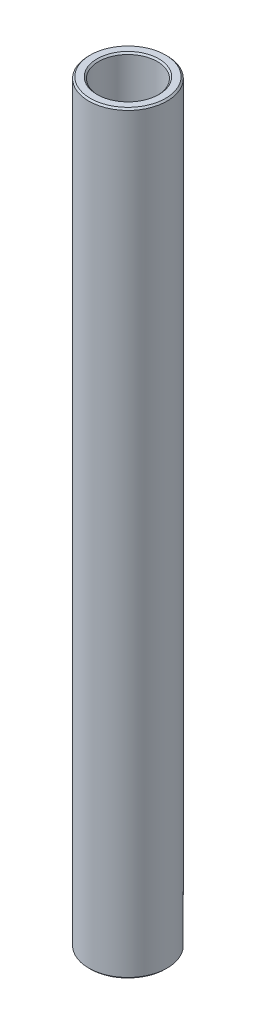
SolidWorks part; units mm, degrees
ref_plane "Front Plane" through (0, 0, 0) normal (0, 0, 1) x (1, 0, 0)
ref_plane "Top Plane" through (0, 0, 0) normal (0, 1, 0) x (1, 0, 0)
ref_plane "Right Plane" through (0, 0, 0) normal (1, 0, 0) x (0, 0, -1)
sketch "Sketch1" plane through (0, 0, 0) normal (0, 0, 1) x (1, 0, 0)
  line L0 (64.0166, -438.6166) -> (64.0166, -316.3791)
  line L1 (64.0166, -316.3791) -> (65.6041, -316.3791)
  line L2 (65.6041, -316.3791) -> (65.6041, -438.6166)
  line L3 (65.6041, -438.6166) -> (64.0166, -438.6166)
  line L6 (59.2541, -448.1416) -> (59.2541, -306.8541) construction
  line L7 (49.1666, -428.2979) -> (-60.8334, -428.2979) construction
  dimension "D1" = 9.525
  dimension "D2" = 9.525
  dimension "D3" = 12.7
  dimension "D4" = 9.525
revolve "Revolve1" add sketch "Sketch1" angle 360 about L6
chamfer "Chamfer1" distance 0.254 angle 45 4 edges at (65.6041, -316.3791, 0) (64.0166, -316.3791, 0) (64.0166, -438.6166, 0) (65.6041, -438.6166, 0)
equation "\"D4@Sketch1\"=\"D1@Sketch1\""
